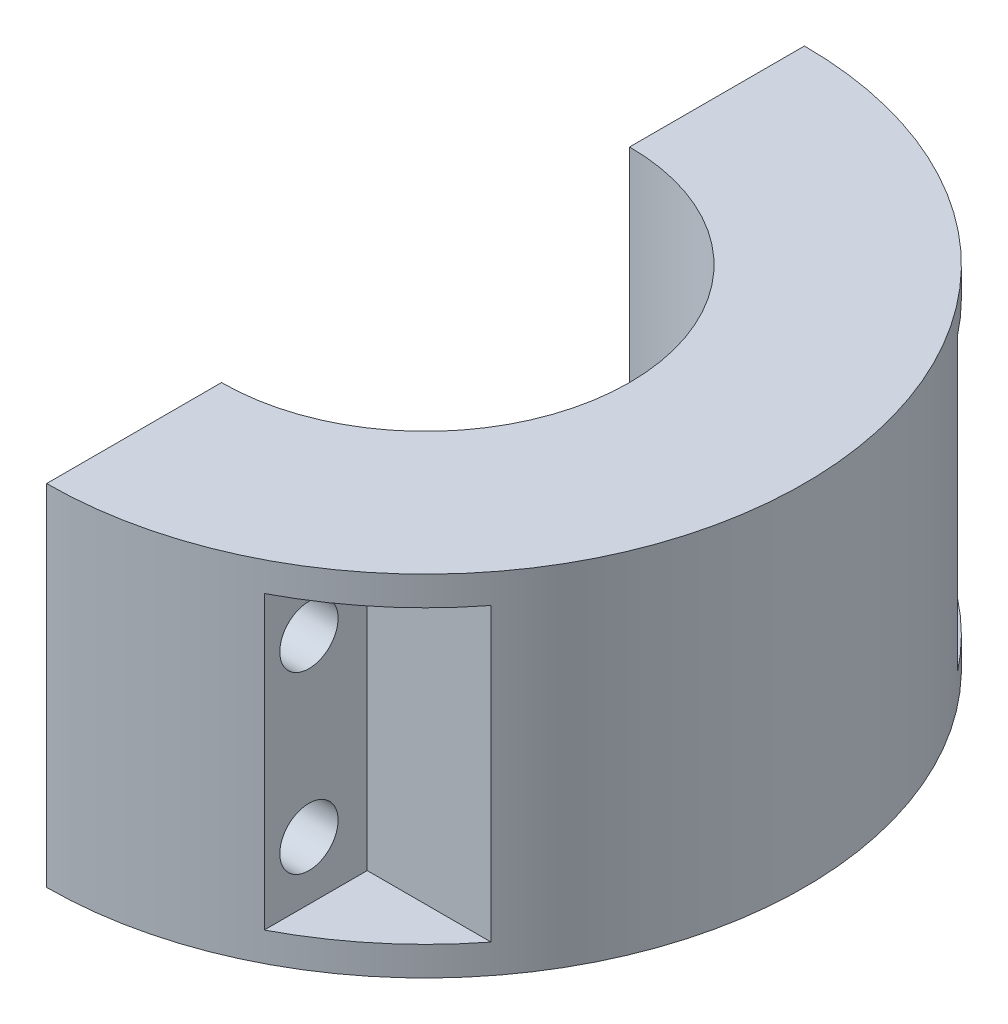
SolidWorks part; units mm, degrees
material "6061-T6 (SS)"
ref_plane "Front Plane" through (0, 0, 0) normal (0, 0, 1) x (1, 0, 0)
ref_plane "Top Plane" through (0, 0, 0) normal (0, 1, 0) x (1, 0, 0)
ref_plane "Right Plane" through (0, 0, 0) normal (1, 0, 0) x (0, 0, -1)
sketch "Sketch1" plane through (0, 0, 0) normal (0, 1, 0) x (1, 0, 0)
  line L0 (0, 82.55) -> (0, 44.45)
  line L1 (0, -44.45) -> (0, -82.55)
  arc A0 (0, -82.55) -> (0, 82.55) centre (0, 0) ccw
  arc A1 (0, -44.45) -> (0, 44.45) centre (0, 0) ccw
  dimension "D1" = 165.1
  dimension "D2" = 88.9
extrude "Boss-Extrude1" add sketch "Sketch1" along normal blind 76.2
sketch "Sketch2" plane through (0, 0, 0) normal (-1, 0, 0) x (0, 0, 1)
  line L0 (-82.55, 76.2) -> (-44.45, 76.2) construction
  line L1 (-82.55, 0) -> (-44.45, 0) construction
  line L3 (44.45, 76.2) -> (82.55, 76.2) construction
  circle A0 centre (-63.5, 57.15) radius 6.35
  circle A1 centre (-63.5, 19.05) radius 6.35
  circle A2 centre (63.5, 19.05) radius 6.35
  circle A3 centre (63.5, 57.15) radius 6.35
  point P8 (0, 0)
  point P9 (0, 0)
  point P10 (0, 0)
  point P11 (0, 0)
  point P12 (-67.8638, 58.1531)
  point P13 (67.0195, 20.8966)
  point P18 (-63.5, 76.2)
  point P21 (63.5, 76.2)
  dimension "D3" = 12.7
  dimension "D4" = 12.7
  dimension "D5" = 12.7
  dimension "D6" = 12.7
  dimension "D1" = 19.05
  dimension "D2" = 19.05
extrude "Cut-Extrude1" cut sketch "Sketch2" against normal through all
ref_plane "Plane1" through (38.1, 0, 0) normal (-1, 0, 0) x (0, 0, 1)
sketch "Sketch3" plane through (38.1, 0, 0) normal (-1, 0, 0) x (0, 0, 1)
  line L0 (44.45, 76.2) -> (82.55, 76.2) construction
  line L1 (76.2, 69.85) -> (50.8, 69.85)
  line L2 (76.2, 69.85) -> (76.2, 6.35)
  line L3 (76.2, 6.35) -> (50.8, 6.35)
  line L4 (50.8, 69.85) -> (50.8, 6.35)
  line L5 (76.2, 69.85) -> (50.8, 6.35) construction
  line L6 (76.2, 6.35) -> (50.8, 69.85) construction
  line L7 (-50.8, 69.85) -> (-76.2, 69.85)
  line L8 (-50.8, 69.85) -> (-50.8, 6.35)
  line L9 (-50.8, 6.35) -> (-76.2, 6.35)
  line L10 (-76.2, 69.85) -> (-76.2, 6.35)
  line L11 (-50.8, 69.85) -> (-76.2, 6.35) construction
  line L12 (-50.8, 6.35) -> (-76.2, 69.85) construction
  line L13 (-82.55, 76.2) -> (-44.45, 76.2) construction
  circle A0 centre (-63.5, 57.15) radius 6.35 construction
  circle A1 centre (63.5, 19.05) radius 6.35 construction
  point P0 (63.5, 38.1)
  point P5 (-63.5, 38.1)
  point P12 (63.5, 76.2)
  point P13 (63.5, 69.85)
  point P16 (-63.5, 76.2)
  point P17 (-63.5, 69.85)
  dimension "D3" = 12.7
  dimension "D4" = 12.7
  dimension "D1" = 25.4
  dimension "D2" = 25.4
extrude "Cut-Extrude2" cut sketch "Sketch3" against normal through all
